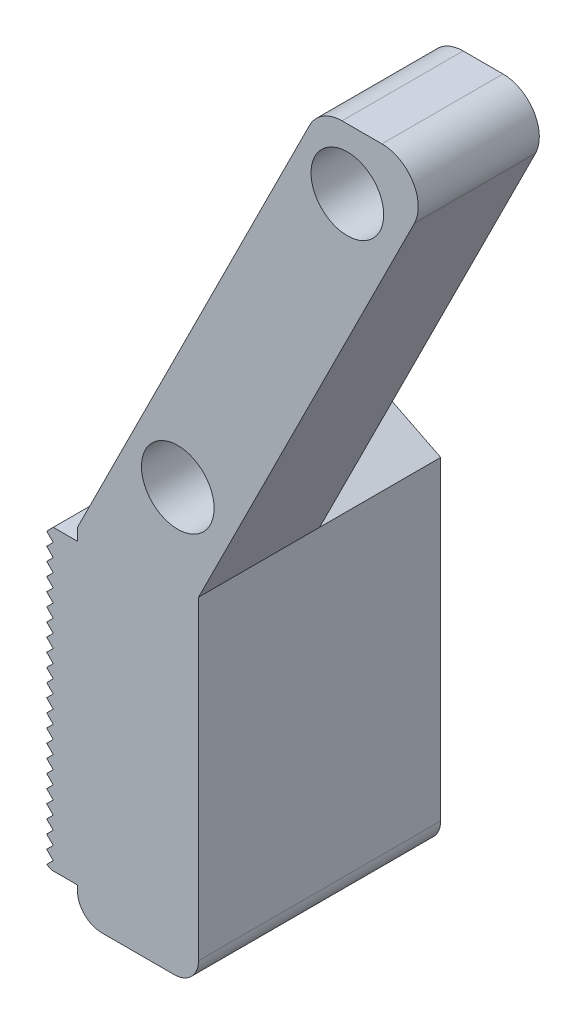
SolidWorks part; units mm, degrees
ref_plane "Front Plane" through (0, 0, 0) normal (0, 0, 1) x (1, 0, 0)
ref_plane "Top Plane" through (0, 0, 0) normal (0, 1, 0) x (1, 0, 0)
ref_plane "Right Plane" through (0, 0, 0) normal (1, 0, 0) x (0, 0, -1)
sketch "Sketch2" plane through (0, 0, 0) normal (0, 0, 1) x (1, 0, 0)
  line L6 (0, 0) -> (-5, 0)
  line L7 (-5, 0) -> (-15, -20)
  line L8 (-15, -20) -> (-15, -34)
  line L9 (0, 0) -> (-10, -20)
  line L12 (-10, -20) -> (-10, -34)
  line L13 (-10, -34) -> (-15, -34)
  circle A3 centre (-3.855, -2.5) radius 1.5
  circle A4 centre (-10.8574, -16.5) radius 1.5
  dimension "D7" = 2.5
  dimension "D9" = 3
  dimension "D8" = 3
  dimension "D1" = 5
  dimension "D2" = 20
  dimension "D3" = 34
  dimension "D4" = 15
  dimension "D5" = 2.33
  dimension "D6" = 3.5
  dimension "D10" = 2.14
extrude "Boss-Extrude1" add sketch "Sketch2" along normal blind 10
sketch "Sketch4" plane through (0, 0, 0) normal (0.8944, -0.4472, 0) x (0, 0, -1)
  line L0 (-5, 0) -> (-5, -22.3607)
  line L1 (-10, 0) -> (0, 0) construction
  line L2 (-10, -22.3607) -> (0, -22.3607) construction
  line L3 (-5, -22.3607) -> (0, -22.3607)
  line L4 (0, -22.3607) -> (0, 0)
  line L5 (0, 0) -> (-5, 0)
extrude "Cut-Extrude1" cut sketch "Sketch4" against normal blind 10
fillet "Fillet1" radius 1.5 2 edges at (-5, 0, 7.5) (0, 0, 7.5)
fillet "Fillet2" radius 1 2 edges at (-10, -34, 5) (-15, -34, 5)
sketch "Sketch5" plane through (0, 0, 10) normal (0, 0, 1) x (1, 0, 0)
  line L0 (-15, -20.5) -> (-16, -20.5)
  line L1 (-15, -20) -> (-15, -33) construction
  line L2 (-16, -20.5) -> (-16.2709, -20.7709)
  line L3 (-16.2709, -20.7709) -> (-16, -21.0418)
  line L4 (-16, -21.0418) -> (-16.2709, -21.3126)
  line L5 (-16.2709, -21.3126) -> (-16, -21.5835)
  line L6 (-16.2709, -22.3962) -> (-16, -22.667)
  line L7 (-16.2709, -21.8544) -> (-16, -22.1253)
  line L8 (-16, -22.1253) -> (-16.2709, -22.3962)
  line L9 (-16, -21.5835) -> (-16.2709, -21.8544)
  line L10 (-16, -23.7506) -> (-16.2709, -24.0214)
  line L11 (-16, -23.2088) -> (-16.2709, -23.4797)
  line L12 (-16, -22.667) -> (-16.2709, -22.9379)
  line L13 (-16.2709, -22.9379) -> (-16, -23.2088)
  line L14 (-16.2709, -23.4797) -> (-16, -23.7506)
  line L15 (-16.2709, -24.0214) -> (-16, -24.2923)
  line L16 (-16, -24.2923) -> (-16.2709, -24.5632)
  line L17 (-16.2709, -24.5632) -> (-16, -24.8341)
  line L18 (-16, -28.6264) -> (-16.2709, -28.8973)
  line L19 (-16, -27.5429) -> (-16.2709, -27.8138)
  line L20 (-16, -25.3758) -> (-16.2709, -25.6467)
  line L21 (-16.2709, -28.8973) -> (-16, -29.1682)
  line L22 (-16, -25.9176) -> (-16.2709, -26.1885)
  line L23 (-16.2709, -27.272) -> (-16, -27.5429)
  line L24 (-16, -26.4594) -> (-16.2709, -26.7302)
  line L25 (-16, -24.8341) -> (-16.2709, -25.105)
  line L26 (-16.2709, -26.7302) -> (-16, -27.0011)
  line L27 (-16.2709, -28.3555) -> (-16, -28.6264)
  line L28 (-16.2709, -25.105) -> (-16, -25.3758)
  line L29 (-16.2709, -26.1885) -> (-16, -26.4594)
  line L30 (-16.2709, -25.6467) -> (-16, -25.9176)
  line L31 (-16, -27.0011) -> (-16.2709, -27.272)
  line L32 (-16.2709, -27.8138) -> (-16, -28.0846)
  line L33 (-16, -28.0846) -> (-16.2709, -28.3555)
  line L36 (-15, -32.79) -> (-16.0708, -32.79)
  line L37 (-16.2709, -32.6896) -> (-16.0708, -32.79)
  line L38 (-16, -29.1682) -> (-16.2709, -29.439)
  line L39 (-15, -32.79) -> (-15, -20.5)
  line L43 (-16.2709, -31.0643) -> (-16, -31.3352)
  line L45 (-16, -31.3352) -> (-16.2709, -31.6061)
  line L47 (-16.2709, -29.9808) -> (-16, -30.2517)
  line L48 (-16, -30.7934) -> (-16.2709, -31.0643)
  line L49 (-16, -29.7099) -> (-16.2709, -29.9808)
  line L50 (-16, -31.877) -> (-16.2709, -32.1478)
  line L52 (-16, -32.4187) -> (-16.2709, -32.6896)
  line L55 (-16.2709, -32.1478) -> (-16, -32.4187)
  line L58 (-16.2709, -29.439) -> (-16, -29.7099)
  line L61 (-16, -30.2517) -> (-16.2709, -30.5226)
  line L62 (-16.2709, -31.6061) -> (-16, -31.877)
  line L64 (-16.2709, -30.5226) -> (-16, -30.7934)
  dimension "D1" = 1
  dimension "D2" = 0.5
  dimension "D3" = 0.21
extrude "Boss-Extrude2" add sketch "Sketch5" against normal up to surface (10 mm away) up to face at (-12.7143, -27.4877, 0)
